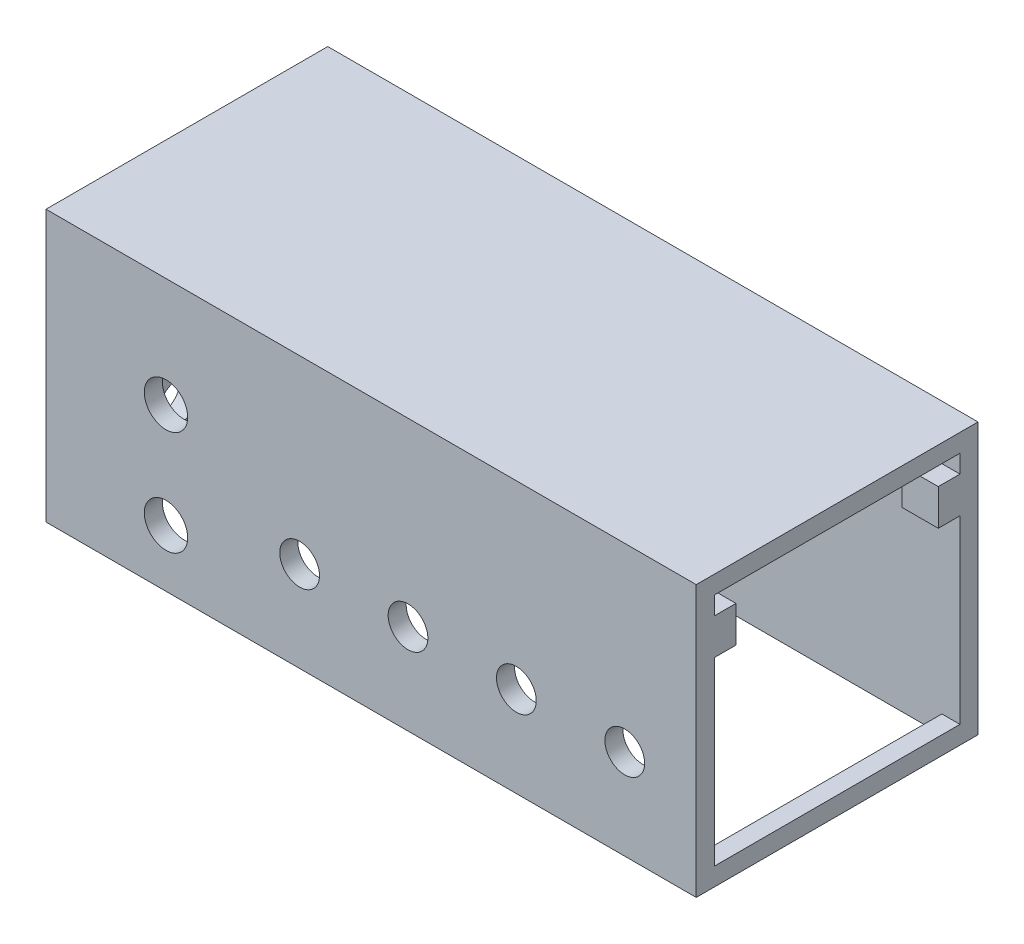
SolidWorks part; units mm, degrees
ref_plane "Front Plane" through (0, 0, 0) normal (0, 0, 1) x (1, 0, 0)
ref_plane "Top Plane" through (0, 0, 0) normal (0, 1, 0) x (1, 0, 0)
ref_plane "Right Plane" through (0, 0, 0) normal (1, 0, 0) x (0, 0, -1)
sketch "Sketch1" plane through (0, 0, 0) normal (0, 1, 0) x (1, 0, 0)
  line L1 (0, 0) -> (180, 0)
  line L2 (0, 0) -> (0, -78)
  line L3 (0, -78) -> (180, -78)
  line L4 (180, 0) -> (180, -78)
  dimension "D1" = 180
  dimension "D2" = 78
extrude "Boss-Extrude1" add sketch "Sketch1" along normal blind 75
sketch "Sketch2" plane through (0, 0, 78) normal (0, 0, 1) x (1, 0, 0)
  line L0 (70.2122, 25) -> (100.2122, 25) construction
  line L1 (100.2122, 25) -> (130.2122, 25) construction
  line L2 (130.2122, 25) -> (160.2122, 25) construction
  line L3 (0, 0) -> (180, 0) construction
  circle A0 centre (160.2122, 25) radius 5.5
  circle A1 centre (100.2122, 25) radius 5.5
  circle A2 centre (130.2122, 25) radius 5.5
  circle A3 centre (70.2122, 25) radius 5.5
  circle A4 centre (33.2191, 44.7389) radius 6
  circle A5 centre (33.2191, 15.8196) radius 6
  dimension "D1" = 30
  dimension "D2" = 12
  dimension "D3" = 11
  dimension "D4" = 25
sketch "Sketch6" plane through (0, 0, 0) normal (1, 0, 0) x (0, 0, -1)
  line L0 (-78, 75) -> (0, 75) construction
  circle A0 centre (-46.3639, 44.6365) radius 5.5
  circle A1 centre (-46.3639, 15.4867) radius 5.5
  point P8 (-49.4935, 21.8105)
  dimension "D1" = 29.1498
  dimension "D2" = 30.3635
sketch "Sketch7" plane through (0, 0, 0) normal (0, 1, 0) x (1, 0, 0)
  line L0 (0, -41.25) -> (0, 41.25) construction
  line L1 (5, -5) -> (175, -5)
  line L2 (5, -5) -> (5, -73)
  line L3 (5, -73) -> (175, -73)
  line L4 (175, -5) -> (175, -73)
  line L5 (180, 0) -> (0, 0) construction
  dimension "D1" = 170
  dimension "D2" = 68
  dimension "D3" = 5
  dimension "D4" = 5
extrude "Cut-Extrude1" cut sketch "Sketch7" along normal blind 70
sketch "Sketch8" plane through (180, 0, 0) normal (1, 0, 0) x (0, 0, -1)
  line L0 (-78, 75) -> (0, 75) construction
  line L1 (-73, 70) -> (-5, 70)
  line L2 (-73, 70) -> (-73, 5)
  line L3 (-73, 5) -> (-5, 5)
  line L4 (-5, 70) -> (-5, 5)
  line L5 (0, 75) -> (0, 0) construction
  line L6 (-78, 0) -> (0, 0) construction
  line L7 (-78, 75) -> (-78, 0) construction
  dimension "D1" = 5
  dimension "D2" = 5
  dimension "D3" = 5
  dimension "D4" = 5
extrude "Cut-Extrude2" cut sketch "Sketch8" against normal blind 5
extrude "Cut-Extrude3" cut sketch "Sketch2" against normal blind 5
extrude "Cut-Extrude5" cut sketch "Sketch6" along normal blind 5
sketch "Sketch9" plane through (0, 0, 73) normal (0, 0, -1) x (-1, 0, 0)
  line L0 (-180, 75) -> (-180, 0) construction
  line L1 (-180, 65) -> (-170, 65)
  line L2 (-180, 65) -> (-180, 55)
  line L3 (-180, 55) -> (-170, 55)
  line L4 (-170, 65) -> (-170, 55)
  line L5 (-180, 75) -> (0, 75) construction
  line L6 (-95, 65) -> (-85, 65)
  line L7 (-95, 65) -> (-95, 55)
  line L8 (-95, 55) -> (-85, 55)
  line L9 (-85, 65) -> (-85, 55)
  line L10 (-15, 65) -> (-5, 65)
  line L11 (-15, 65) -> (-15, 55)
  line L12 (-15, 55) -> (-5, 55)
  line L13 (-5, 65) -> (-5, 55)
  line L14 (0, 75) -> (-180, 75) construction
  line L15 (0, 41.25) -> (0, -41.25) construction
  point P16 (-90, 75)
  point P21 (-90, 65)
  dimension "D1" = 10
  dimension "D2" = 10
  dimension "D3" = 10
  dimension "D4" = 10
  dimension "D5" = 10
  dimension "D6" = 5
extrude "Boss-Extrude2" add sketch "Sketch9" along normal blind 6
ref_plane "Plane1" through (0, 0, 39) normal (0, 0, 1) x (1, 0, 0)
mirror "Mirror1" about plane through (0, 0, 39) normal (0, 0, 1) of "Boss-Extrude2"
